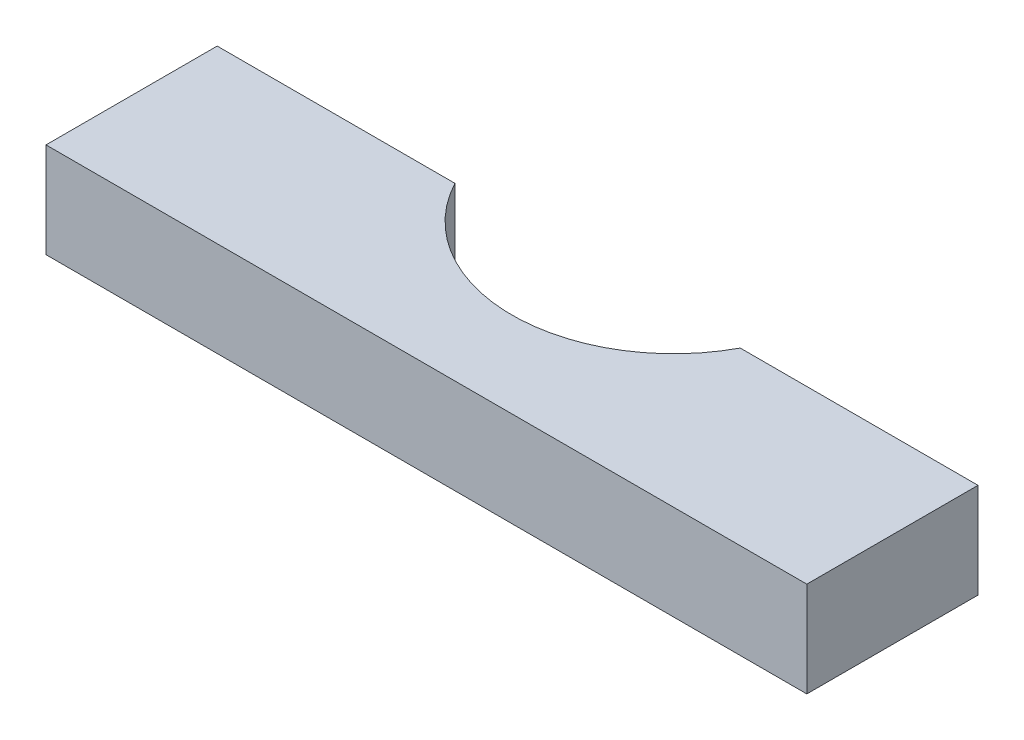
SolidWorks part; units mm, degrees
ref_plane "Front Plane" through (0, 0, 0) normal (0, 0, 1) x (1, 0, 0)
ref_plane "Top Plane" through (0, 0, 0) normal (0, 1, 0) x (1, 0, 0)
ref_plane "Right Plane" through (0, 0, 0) normal (1, 0, 0) x (0, 0, -1)
sketch "Sketch1" plane through (0, 0, 0) normal (0, 1, 0) x (1, 0, 0)
  line L1 (-25.4, 5.715) -> (25.4, 5.715)
  line L2 (-25.4, 5.715) -> (-25.4, -5.715)
  line L3 (-25.4, -5.715) -> (25.4, -5.715)
  line L4 (25.4, 5.715) -> (25.4, -5.715)
  line L5 (-25.4, 5.715) -> (25.4, -5.715) construction
  line L6 (-25.4, -5.715) -> (25.4, 5.715) construction
  point P0 (0, 0)
  dimension "D1" = 11.43
  dimension "D2" = 50.8
extrude "Boss-Extrude1" add sketch "Sketch1" along normal blind 6.35
ref_plane "Plane1" through (0, 6.35, 0) normal (0, 1, 0) x (1, 0, 0)
sketch "Sketch2" plane through (0, 6.35, 0) normal (0, 1, 0) x (1, 0, 0)
  line L0 (25.4, 5.715) -> (-25.4, 5.715) construction
  line L1 (-9.525, 5.715) -> (9.525, 5.715)
  arc A0 (-9.525, 5.715) -> (9.525, 5.715) centre (0, 10.795) ccw
  point P0 (0, 5.715)
  point P6 (0, 5.715)
  dimension "D1" = 19.05
extrude "Cut-Extrude1" cut sketch "Sketch2" against normal through all
